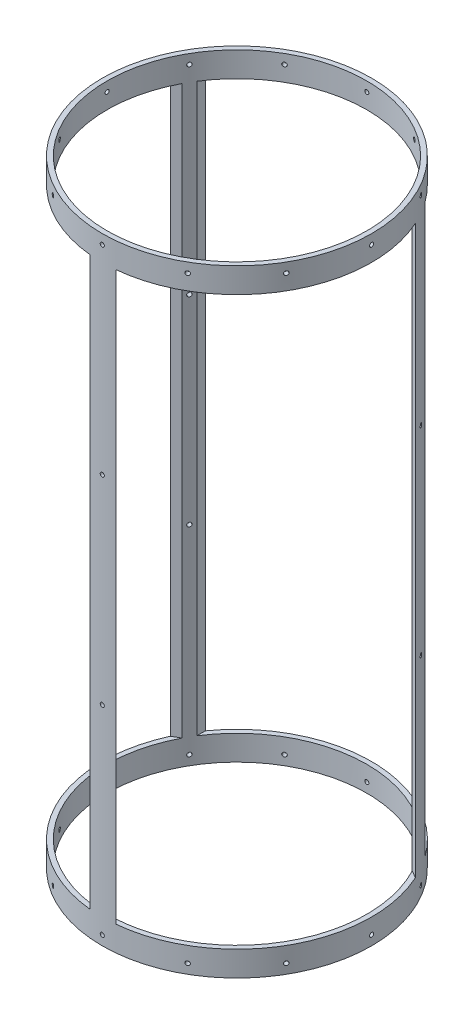
SolidWorks part; units mm, degrees
material "6061-T6 (SS)"
ref_plane "Front Plane" through (0, 0, 0) normal (0, 0, 1) x (1, 0, 0)
ref_plane "Top Plane" through (0, 0, 0) normal (0, 1, 0) x (1, 0, 0)
ref_plane "Right Plane" through (0, 0, 0) normal (1, 0, 0) x (0, 0, -1)
sketch "Sketch1" plane through (0, 0, 0) normal (0, 1, 0) x (1, 0, 0)
  circle A0 centre (0, 0) radius 88.9
  circle A1 centre (0, 0) radius 85.725
  dimension "D1" = 177.8
  dimension "D2" = 171.45
extrude "Boss-Extrude1" add sketch "Sketch1" along normal mid plane 407.162
sketch "Sketch2" plane through (0, 0, 0) normal (0, 0, 1) x (1, 0, 0)
  line L0 (85.725, 203.581) -> (-85.725, 203.581) construction
  line L1 (-72.39, -187.071) -> (72.39, -187.071)
  line L2 (-72.39, -187.071) -> (-72.39, 187.071)
  line L3 (-72.39, 187.071) -> (72.39, 187.071)
  line L4 (72.39, -187.071) -> (72.39, 187.071)
  line L5 (-72.39, -187.071) -> (72.39, 187.071) construction
  line L6 (-72.39, 187.071) -> (72.39, -187.071) construction
  line L7 (88.9, -203.581) -> (88.9, 203.581) construction
  point P0 (0, 0)
  dimension "D1" = 16.51
  dimension "D2" = 16.51
extrude "Cut-Extrude1" cut sketch "Sketch2" against normal up to surface (51.6033 mm away)
pattern_circular "CirPattern1" count 3 over 360 about axis through (0, 0, 0) along (0, 1, 0) of "Cut-Extrude1"
ref_plane "Plane1" through (88.9, 0, 0) normal (1, 0, 0) x (0, 0, -1)
sketch "Sketch4" plane through (88.9, 0, 0) normal (1, 0, 0) x (0, 0, -1)
  line L0 (0, 97.79) -> (0, -97.79) construction
  line L1 (88.9, 203.581) -> (-88.9, 203.581) construction
  circle A0 centre (0, 197.231) radius 1.3525
  dimension "D1" = 2.7051
  dimension "D2" = 6.35
extrude "Cut-Extrude3" cut sketch "Sketch4" against normal blind 15.24
pattern_circular "CirPattern3" count 12 over 360 about axis through (0, 203.581, 0) along (0, -1, 0) of "Cut-Extrude3"
mirror "Mirror1" about plane through (0, 0, 0) normal (0, 1, 0) of "Cut-Extrude3", "CirPattern3"
ref_plane "Plane2" through (0, 0, 88.9) normal (0, 0, 1) x (1, 0, 0)
sketch "Sketch5" plane through (0, 0, 88.9) normal (0, 0, 1) x (1, 0, 0)
  circle A0 centre (0, -65.7606) radius 1.3526
  circle A1 centre (0, 65.7606) radius 1.3526
  circle A2 centre (0, 197.231) radius 1.3525 construction
  circle A3 centre (0, -197.231) radius 1.3525 construction
  dimension "D1" = 131.4704
  dimension "D2" = 131.4704
  dimension "D3" = 2.7051
  dimension "D4" = 2.7051
extrude "Cut-Extrude4" cut sketch "Sketch5" against normal blind 46.482
pattern_circular "CirPattern4" count 3 over 360 about axis through (0, 203.581, 0) along (0, -1, 0) of "Cut-Extrude4"
